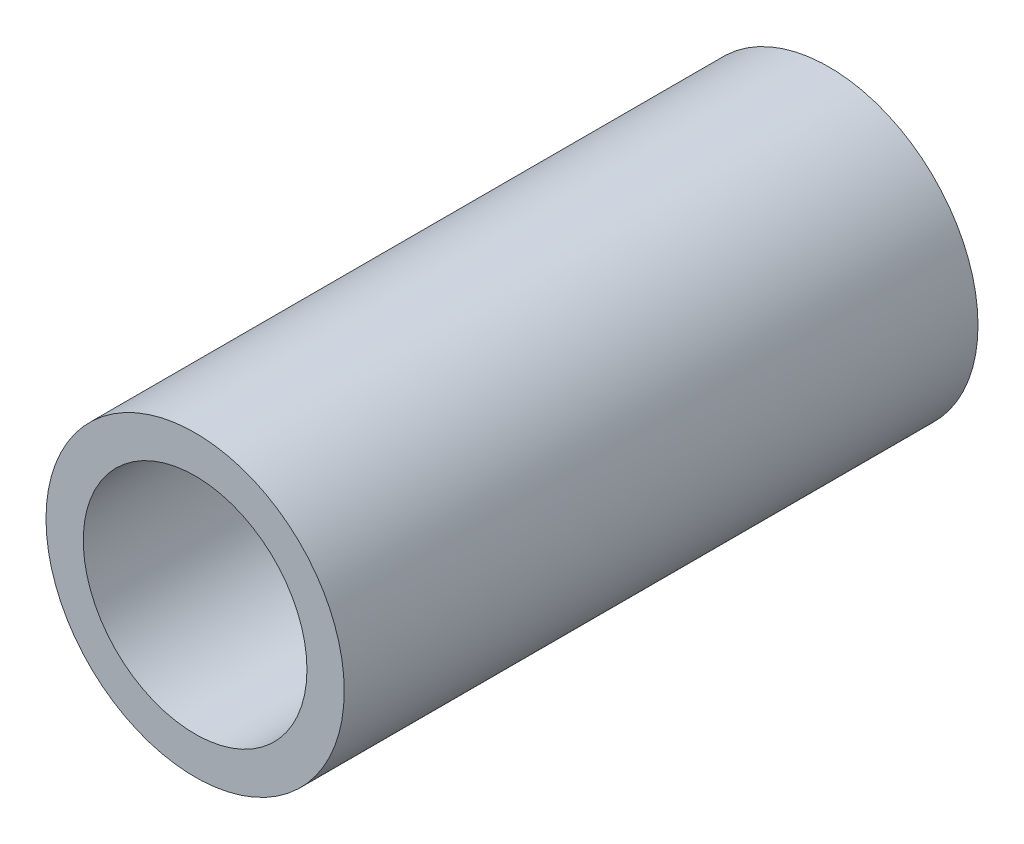
SolidWorks part; units mm, degrees
ref_plane "正面" through (0, 0, 0) normal (0, 0, 1) x (1, 0, 0)
ref_plane "平面" through (0, 0, 0) normal (0, 1, 0) x (1, 0, 0)
ref_plane "右側面" through (0, 0, 0) normal (1, 0, 0) x (0, 0, -1)
sketch "ｽｹｯﾁ1" plane through (0, 0, 0) normal (0, 0, 1) x (1, 0, 0)
  circle A0 centre (0, 0) radius 2
  circle A1 centre (0, 0) radius 1.5
  dimension "D1" = 3
  dimension "D2" = 4
extrude "ﾎﾞｽ - 押し出し1" add sketch "ｽｹｯﾁ1" along normal blind 8.5
